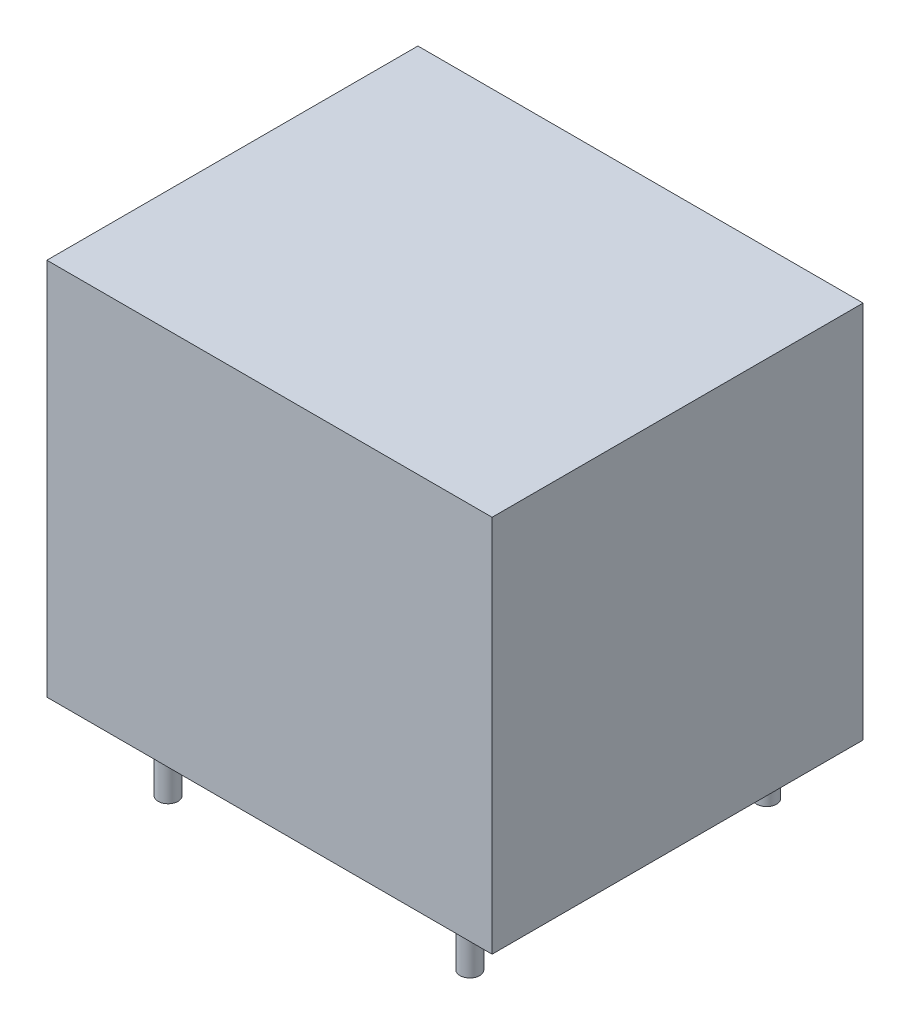
SolidWorks part; units mm, degrees
ref_plane "Plan de face" through (0, 0, 0) normal (0, 0, 1) x (1, 0, 0)
ref_plane "Plan de dessus" through (0, 0, 0) normal (0, 1, 0) x (1, 0, 0)
ref_plane "Plan de droite" through (0, 0, 0) normal (1, 0, 0) x (0, 0, -1)
sketch "Esquisse1" plane through (0, 0, 0) normal (0, 1, 0) x (1, 0, 0)
  line L0 (-14.6891, 0) -> (14.3684, 0) construction
  line L1 (0, 11.065) -> (0, -10.1669) construction
  line L3 (-9, 7.5) -> (9, 7.5)
  line L4 (-9, 7.5) -> (-9, -7.5)
  line L5 (-9, -7.5) -> (9, -7.5)
  line L6 (9, 7.5) -> (9, -7.5)
  dimension "D1" = 18
  dimension "D2" = 15
extrude "Boss.-Extru.1" add sketch "Esquisse1" along normal blind 15.3
sketch "Esquisse2" plane through (0, 0, 0) normal (0, -1, 0) x (-1, 0, 0)
  line L0 (10.9417, 0) -> (-10.5317, 0) construction
  line L2 (7.6, -1.4567) -> (7.6, 1.4567) construction
  line L3 (9, 7.5) -> (9, -7.5) construction
  line L4 (5.6, -8.2764) -> (5.6, 8.8807) construction
  line L5 (-6.6, -8.2764) -> (-6.6, 8.2764) construction
  circle A0 centre (7.6, 0) radius 0.4
  circle A1 centre (5.6, -6) radius 0.4
  circle A2 centre (5.6, 6) radius 0.4
  circle A3 centre (-6.6, -6) radius 0.4
  circle A4 centre (-6.6, 6) radius 0.4
  dimension "D4" = 0.8
  dimension "D5" = 0.8
  dimension "D8" = 0.8
  dimension "D9" = 0.8
  dimension "D10" = 0.8
  dimension "D1" = 1.4
  dimension "D2" = 2
  dimension "D3" = 12.2
  dimension "D6" = 12
  dimension "D7" = 12
extrude "Boss.-Extru.2" add sketch "Esquisse2" along normal blind 2.5
